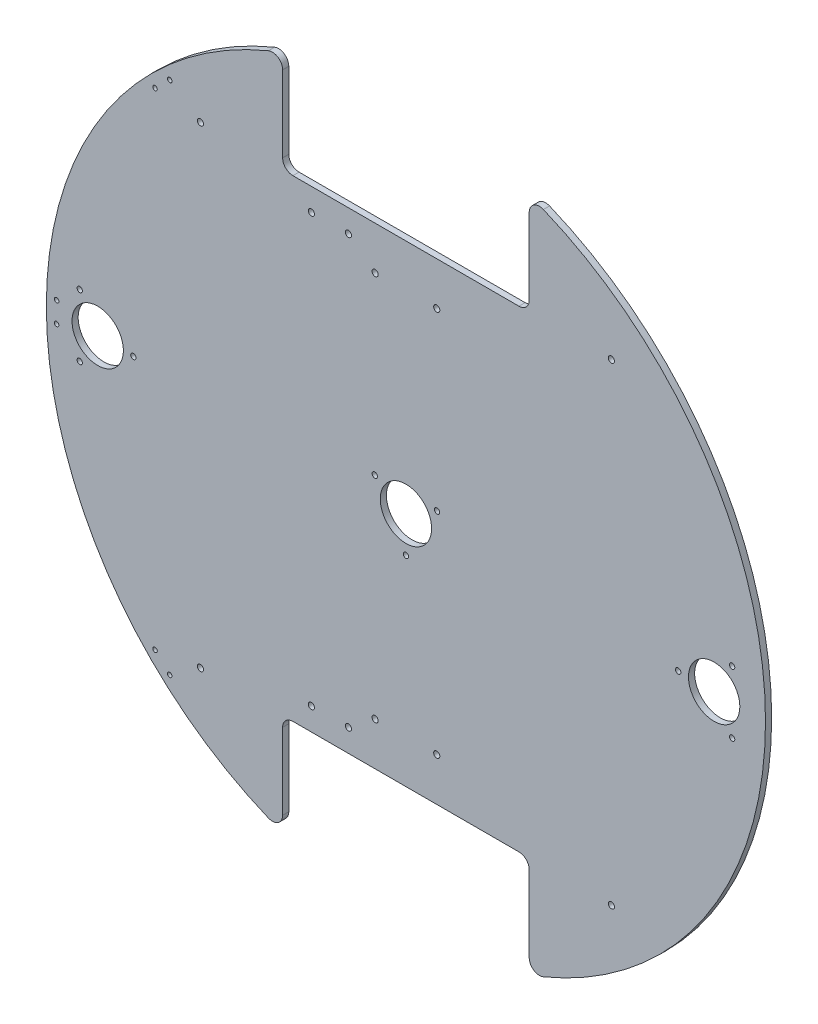
SolidWorks part; units mm, degrees
material "ｱｸﾘﾙ (中-上級の耐衝撃性)"
ref_plane "正面" through (0, 0, 0) normal (0, 0, 1) x (1, 0, 0)
ref_plane "平面" through (0, 0, 0) normal (0, 1, 0) x (1, 0, 0)
ref_plane "右側面" through (0, 0, 0) normal (1, 0, 0) x (0, 0, -1)
sketch "ｽｹｯﾁ1" plane through (0, 0, 0) normal (0, 0, 1) x (1, 0, 0)
  circle A0 centre (0, 0) radius 175
  dimension "D1" = 350
extrude "ﾎﾞｽ - 押し出し1" add sketch "ｽｹｯﾁ1" along normal blind 3
sketch "ｽｹｯﾁ2" plane through (0, 0, 3) normal (0, 0, 1) x (1, 0, 0)
  line L0 (0, 0) -> (175, 0)
  line L1 (0, 0) -> (-175, 0)
  line L2 (0, 0) -> (0, 115)
  line L3 (0, 0) -> (0, -115)
  line L4 (0, 115) -> (60, 115)
  line L5 (0, 115) -> (0, 175)
  line L6 (0, 175) -> (60, 175)
  line L7 (60, 115) -> (60, 175)
  line L8 (0, 115) -> (-60, 115)
  line L9 (0, 115) -> (0, 175)
  line L10 (0, 175) -> (-60, 175)
  line L11 (-60, 115) -> (-60, 175)
  line L13 (0, -115) -> (60, -115)
  line L14 (0, -115) -> (0, -175)
  line L15 (0, -175) -> (60, -175)
  line L16 (60, -115) -> (60, -175)
  line L17 (0, -115) -> (-60, -115)
  line L18 (0, -115) -> (0, -175)
  line L19 (0, -175) -> (-60, -175)
  line L20 (-60, -115) -> (-60, -175)
  circle A0 centre (0, 0) radius 175 construction
  circle M1 centre (0, 0) radius 175
  dimension "D1" = 115
  dimension "D2" = 60
  dimension "D3" = 60
  dimension "D4" = 60
  dimension "D5" = 115
  dimension "D6" = 60
extrude "ｶｯﾄ - 押し出し1" cut sketch "ｽｹｯﾁ2" against normal blind 3 contours L11 L8 L5 M1 | L4 L7 L5 M1 | L17 L20 L14 M1 | L16 L13 L14 M1
fillet "ﾌｨﾚｯﾄ1" radius 5 1 edges at (-60, 164.3928, 1.5)
fillet "ﾌｨﾚｯﾄ2" radius 5 3 edges at (60, 115, 1.5) (60, 164.3928, 1.5) (-60, 115, 1.5)
fillet "ﾌｨﾚｯﾄ3" radius 5 4 edges at (-60, -164.3928, 1.5) (-60, -115, 1.5) (60, -164.3928, 1.5) (60, -115, 1.5)
sketch "ｽｹｯﾁ5" plane through (0, 0, 3) normal (0, 0, 1) x (1, 0, 0)
  line L0 (0, 115) -> (-100, 115)
  line L1 (55, 115) -> (-55, 115) construction
  line L2 (0, 115) -> (100, 115)
  line L3 (0, -115) -> (100, -115)
  line L4 (55, -115) -> (-55, -115) construction
  line L5 (100, -115) -> (-100, -115)
  circle A0 centre (-100, -115) radius 1.5
  circle A1 centre (100, -115) radius 1.5
  circle A2 centre (100, 115) radius 1.5
  circle A3 centre (-100, 115) radius 1.5
  dimension "D3" = 3
  dimension "D4" = 3
  dimension "D5" = 3
  dimension "D6" = 3
  dimension "D1" = 100
  dimension "D2" = 100
extrude "ｶｯﾄ - 押し出し4" cut sketch "ｽｹｯﾁ5" against normal blind 3 contours A1 | A0 | A3 | A2
sketch "ｽｹｯﾁ10" plane through (0, 0, 3) normal (0, 0, 1) x (1, 0, 0)
  line L0 (0, 0) -> (-150, 0)
  line L1 (0, 0) -> (150, 0)
  line L2 (-150, 0) -> (-158.75, 15.1554)
  line L3 (-150, 0) -> (-158.75, -15.1554)
  line L4 (-150, 0) -> (-132.6329, 0)
  line L5 (0, 0) -> (15.1554, 8.75)
  line L6 (0, 0) -> (-15.1554, 8.75)
  line L7 (0, 0) -> (0, -17.5)
  line L8 (150, 0) -> (158.75, 15.1554)
  line L9 (150, 0) -> (132.5, 0)
  line L10 (150, 0) -> (158.75, -15.1554)
  circle A0 centre (-150, 0) radius 12.5
  circle A1 centre (150, 0) radius 12.5
  circle A2 centre (0, 0) radius 12.5
  circle A3 centre (-150, 0) radius 17.5
  circle A4 centre (0, 0) radius 17.5
  circle A5 centre (150, 0) radius 17.5
  circle A6 centre (132.5, 0) radius 1.3
  circle A7 centre (158.75, 15.1554) radius 1.3
  circle A8 centre (158.75, -15.1554) radius 1.3
  circle A9 centre (-15.1554, 8.75) radius 1.3
  circle A10 centre (15.1554, 8.75) radius 1.3
  circle A11 centre (0, -17.5) radius 1.3
  circle A12 centre (-158.75, 15.1554) radius 1.3
  circle A13 centre (-158.75, -15.1554) radius 1.3
  circle A14 centre (-132.6329, 0) radius 1.3
  dimension "D3" = 25
  dimension "D4" = 25
  dimension "D5" = 25
  dimension "D6" = 35
  dimension "D7" = 35
  dimension "D8" = 35
  dimension "D15" = 2.6
  dimension "D16" = 2.6
  dimension "D17" = 2.6
  dimension "D18" = 2.6
  dimension "D19" = 2.6
  dimension "D20" = 2.6
  dimension "D21" = 2.6
  dimension "D22" = 2.6
  dimension "D23" = 2.6
  dimension "D1" = 150
  dimension "D2" = 150
  dimension "D9" = 120
  dimension "D10" = 120
  dimension "D11" = 120
  dimension "D12" = 120
  dimension "D13" = 120
  dimension "D14" = 120
sketch "ｽｹｯﾁ12" plane through (0, 0, 3) normal (0, 0, 1) x (1, 0, 0)
  line L0 (0, 115) -> (0, 94)
  line L1 (55, 115) -> (-55, 115) construction
  line L2 (0, 94) -> (15, 94)
  line L3 (0, 94) -> (-15, 94)
  line L7 (0, -115) -> (0, -94)
  line L8 (55, -115) -> (-55, -115) construction
  line L9 (0, -94) -> (15, -94)
  line L10 (0, -94) -> (-15, -94)
  circle A0 centre (-15, 94) radius 1.5
  circle A1 centre (15, 94) radius 1.5
  circle A6 centre (-15, -94) radius 1.5
  circle A7 centre (15, -94) radius 1.5
  dimension "D5" = 3
  dimension "D6" = 3
  dimension "D7" = 15
  dimension "D13" = 3
  dimension "D14" = 3
  dimension "D1" = 21
  dimension "D2" = 15
  dimension "D3" = 15
  dimension "D4" = 15
  dimension "D9" = 21
sketch "ｽｹｯﾁ13" plane through (0, 0, 3) normal (0, 0, 1) x (1, 0, 0)
  line L0 (0, -115) -> (-25, -115)
  line L1 (55, -115) -> (-55, -115) construction
  line L2 (-25, -115) -> (-25, -104)
  line L3 (-46, 104) -> (-28, 104)
  line L4 (0, 115) -> (-28, 115)
  line L5 (-28, -104) -> (-46, -104)
  line L6 (-28, 104) -> (-27.8272, 103.8289)
  line L7 (0, 115) -> (0, -115)
  line L9 (55, 115) -> (-55, 115) construction
  line L10 (-28, 115) -> (-28, 104)
  line L12 (-28, 104) -> (-46, 104)
  circle A1 centre (-28, -104) radius 1.5
  circle A2 centre (-46, -104) radius 1.5
  circle A4 centre (-46, 104) radius 1.5
  circle A7 centre (-28, 104) radius 1.5
  dimension "D8" = 3
  dimension "D9" = 3
  dimension "D13" = 3
  dimension "D14" = 3
  dimension "D1" = 25
  dimension "D2" = 11
  dimension "D3" = 3
  dimension "D4" = 18
  dimension "D5" = 18
  dimension "D10" = 28
  dimension "D11" = 11
extrude "ｶｯﾄ - 押し出し13" cut sketch "ｽｹｯﾁ10" against normal blind 10 contours A12 | A0 | A13 | A14 | A2 | A9 | A10 | A11 | A6 | A1 | A7 | A8
sketch "ｽｹｯﾁ14" plane through (0, 0, 3) normal (0, 0, 1) x (1, 0, 0)
  line L0 (0, 0) -> (-170, 0)
  line L1 (-170, 0) -> (-170, 5)
  line L2 (-170, 0) -> (-170, -5)
  line L3 (0, 0) -> (-118.5181, 121.8748)
  line L4 (0, 0) -> (-118.5181, -121.8748)
  line L5 (-118.5181, 121.8748) -> (-114.9335, 125.3606)
  line L6 (-118.5181, 121.8748) -> (-122.1026, 118.389)
  line L7 (-118.5181, -121.8748) -> (-122.1026, -118.389)
  line L8 (-118.5181, -121.8748) -> (-114.9335, -125.3606)
  circle A0 centre (-170, 5) radius 1.1
  circle A1 centre (-170, -5) radius 1.1
  circle A2 centre (-114.9335, 125.3606) radius 1.1
  circle A3 centre (-122.1026, 118.389) radius 1.1
  circle A4 centre (-122.1026, -118.389) radius 1.1
  circle A5 centre (-114.9335, -125.3606) radius 1.1
  dimension "D4" = 2.2
  dimension "D5" = 2.2
  dimension "D14" = 2.2
  dimension "D15" = 2.2
  dimension "D16" = 2.2
  dimension "D17" = 2.2
  dimension "D1" = 170
  dimension "D2" = 5
  dimension "D3" = 5
  dimension "D6" = 45.8
  dimension "D7" = 45.8
  dimension "D8" = 170
  dimension "D9" = 170
  dimension "D10" = 5
  dimension "D11" = 5
  dimension "D12" = 5
  dimension "D13" = 5
extrude "ｶｯﾄ - 押し出し14" cut sketch "ｽｹｯﾁ14" against normal blind 10 contours A4 | A5 | A0 | A1 | A2 | A3
extrude "ｶｯﾄ - 押し出し17" cut sketch "ｽｹｯﾁ12" against normal blind 10 contours A6 | A7 | A0 | A1
extrude "ｶｯﾄ - 押し出し18" cut sketch "ｽｹｯﾁ13" against normal blind 5 contours A2 | A1 | A4 | A7
